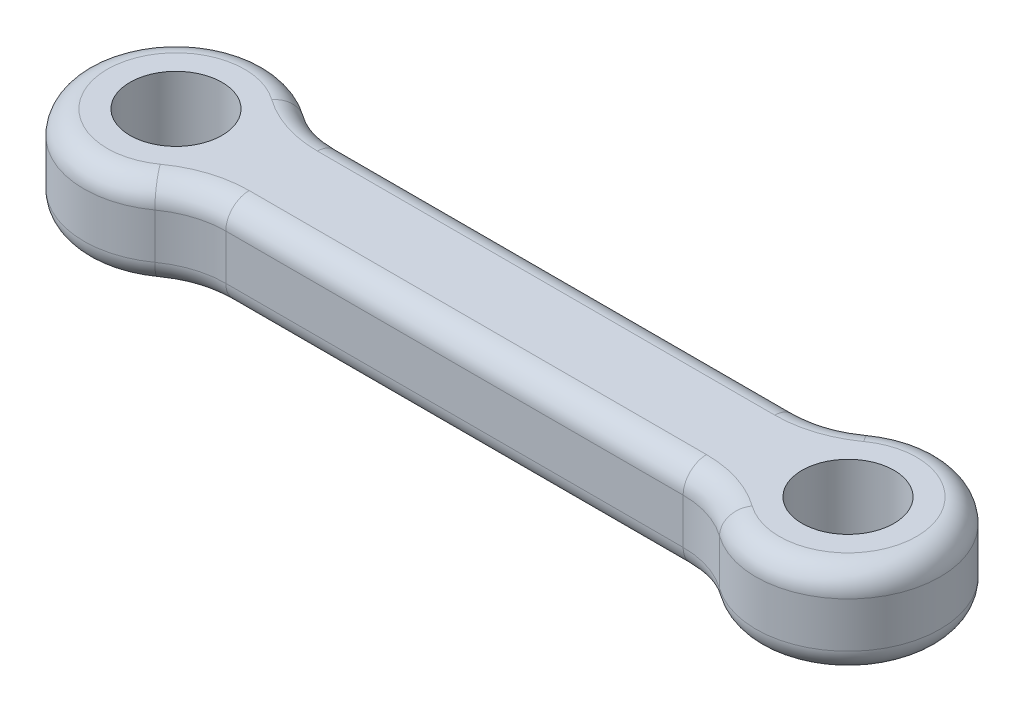
SolidWorks part; units mm, degrees
ref_plane "Front Plane" through (0, 0, 0) normal (0, 0, 1) x (1, 0, 0)
ref_plane "Top Plane" through (0, 0, 0) normal (0, 1, 0) x (1, 0, 0)
ref_plane "Right Plane" through (0, 0, 0) normal (1, 0, 0) x (0, 0, -1)
sketch "Sketch1" plane through (0, 0, 0) normal (0, 1, 0) x (1, 0, 0)
  line L0 (-18.25, 0) -> (18.25, 0) construction
  line L1 (-6.5908, -6.25) -> (43.0908, -6.25)
  line L2 (-6.5908, 6.25) -> (43.0908, 6.25)
  line L3 (-12.4204, -8.125) -> (-12.4204, 8.125) construction
  line L4 (-6.5908, -6.25) -> (-6.5908, 6.25) construction
  line L5 (18.25, -6.25) -> (18.25, 6.25) construction
  arc A0 (-12.4204, 8.125) -> (-12.4204, -8.125) centre (-18.25, 0) ccw
  arc A1 (-12.4204, -8.125) -> (-6.5908, -6.25) centre (-6.5908, -16.25) cw
  arc A2 (-12.4204, 8.125) -> (-6.5908, 6.25) centre (-6.5908, 16.25) ccw
  circle A3 centre (-18.25, 0) radius 5
  circle A4 centre (54.75, 0) radius 5
  arc A5 (48.9204, -8.125) -> (43.0908, -6.25) centre (43.0908, -16.25) ccw
  arc A6 (48.9204, 8.125) -> (48.9204, -8.125) centre (54.75, 0) cw
  arc A7 (48.9204, 8.125) -> (43.0908, 6.25) centre (43.0908, 16.25) cw
  dimension "D3" = 10
  dimension "D4" = 12.5
  dimension "D5" = 10
  dimension "D2" = 10
  dimension "D1" = 36.5
extrude "Boss-Extrude1" add sketch "Sketch1" along normal blind 10
fillet "Fillet1" radius 2.54 16 edges at (-28.25, 0, 0) (-9.6526, 0, 6.7303) (18.25, 0, 6.25) (46.1526, 0, 6.7303) (64.75, 0, 0) (46.1526, 0, -6.7303) (18.25, 0, -6.25) (-9.6526, 0, -6.7303) (18.25, 10, -6.25) (46.1526, 10, -6.7303) (64.75, 10, 0) (46.1526, 10, 6.7303) (18.25, 10, 6.25) (-9.6526, 10, 6.7303) (-28.25, 10, 0) (-9.6526, 10, -6.7303)
scale "Scale1" scale about centroid uniform scaling yes scale factor 0.66
